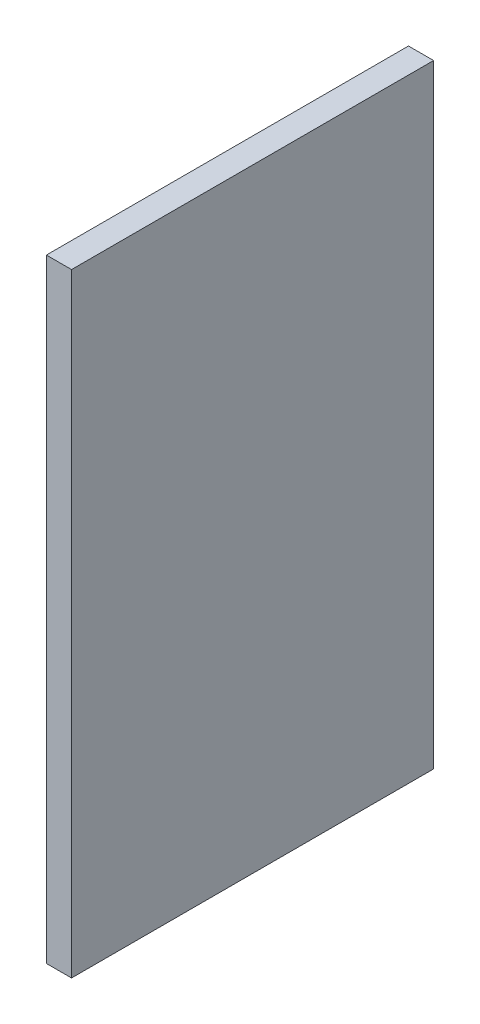
SolidWorks part; units mm, degrees
ref_plane "Front Plane" through (0, 0, 0) normal (0, 0, 1) x (1, 0, 0)
ref_plane "Top Plane" through (0, 0, 0) normal (0, 1, 0) x (1, 0, 0)
ref_plane "Right Plane" through (0, 0, 0) normal (1, 0, 0) x (0, 0, -1)
sketch "Sketch2" plane through (0, 0, -331.8) normal (0, 0, 1) x (1, 0, 0)
  line L0 (-117.6, -98) -> (-122.6, -98)
  line L1 (-117.6, -98) -> (-117.6, -220)
  line L2 (-122.6, -98) -> (-122.6, -220)
  line L3 (-117.6, -220) -> (-122.6, -220)
  line L6 (-249.6, -98) -> (0, -98) construction
  line L8 (-183.6, -220) -> (-249.6, -220) construction
  line L9 (-122.6, -98) -> (-122.6, -350.4) construction
  dimension "D1" = 5
extrude "Boss-Extrude1" add sketch "Sketch2" along normal blind 72
